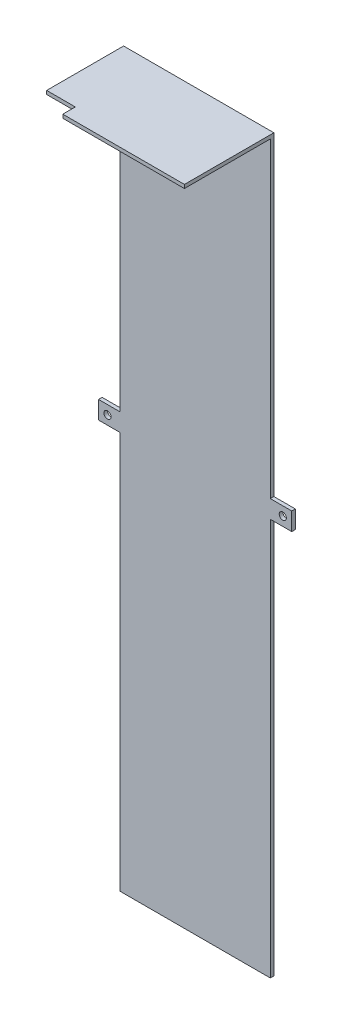
SolidWorks part; units mm, degrees
ref_plane "Alzado" through (0, 0, 0) normal (0, 0, 1) x (1, 0, 0)
ref_plane "Planta" through (0, 0, 0) normal (0, 1, 0) x (1, 0, 0)
ref_plane "Vista lateral" through (0, 0, 0) normal (1, 0, 0) x (0, 0, -1)
sketch "Sketch1" plane through (0, 0, 0) normal (0, 1, 0) x (1, 0, 0)
  line L1 (-16.6842, 5.7368) -> (25.3158, 5.7368)
  line L2 (-16.6842, 5.7368) -> (-16.6842, -19.2632)
  line L3 (-16.6842, -19.2632) -> (25.3158, -19.2632)
  line L4 (25.3158, 5.7368) -> (25.3158, -19.2632)
  dimension "D1" = 42
  dimension "D2" = 25
extrude "Boss-Extrude1" add sketch "Sketch1" along normal blind 1
sketch "Sketch2" plane through (0, 1, 0) normal (0, 1, 0) x (1, 0, 0)
  line L0 (-16.6842, 5.7368) -> (-16.6842, -19.2632) construction
  line L1 (25.3158, 5.7368) -> (-16.6842, 5.7368)
  line L2 (25.3158, 5.7368) -> (25.3158, 4.7368)
  line L3 (25.3158, 4.7368) -> (-16.6842, 4.7368)
  line L4 (-16.6842, 5.7368) -> (-16.6842, 4.7368)
  dimension "D1" = 1
extrude "Boss-Extrude2" add sketch "Sketch2" against normal blind 179
sketch "Sketch3" plane through (0, -178, 0) normal (0, -1, 0) x (1, 0, 0)
  line L1 (25.3158, -5.7368) -> (-16.6842, -5.7368)
  line L2 (25.3158, -5.7368) -> (25.3158, -4.7368)
  line L3 (25.3158, -4.7368) -> (-16.6842, -4.7368)
  line L4 (-16.6842, -5.7368) -> (-16.6842, -4.7368)
extrude "Boss-Extrude3" add sketch "Sketch3" along normal blind 2.1
sketch "Sketch4" plane through (0, 0, -4.7368) normal (0, 0, 1) x (1, 0, 0)
  line L0 (-16.6842, -180.1) -> (-16.6842, 0) construction
  line L1 (25.3158, -180.1) -> (-16.6842, -180.1)
  line L2 (25.3158, -180.1) -> (25.3158, -179.1)
  line L3 (25.3158, -179.1) -> (-16.6842, -179.1)
  line L4 (-16.6842, -180.1) -> (-16.6842, -179.1)
  dimension "D1" = 1
extrude "Boss-Extrude4" add sketch "Sketch4" along normal blind 15
sketch "Sketch6" plane through (0, -180.1, 0) normal (0, -1, 0) x (1, 0, 0)
  line L0 (-16.6842, 10.2632) -> (-16.6842, -5.7368) construction
  line L2 (25.3158, -5.7368) -> (25.3158, 10.2632) construction
  circle A0 centre (-6.6842, 3.5932) radius 1.25
  circle A1 centre (15.3158, 3.5932) radius 1.25
  dimension "D2" = 10
  dimension "D1" = 10
extrude "Cut-Extrude1" cut sketch "Sketch6" against normal blind 15
sketch "Sketch7" plane through (0, -180.1, 0) normal (0, -1, 0) x (1, 0, 0)
  line L1 (25.3158, -5.7368) -> (25.3158, 10.2632) construction
  line L2 (-16.6842, 10.2632) -> (25.3158, 10.2632)
  line L3 (-16.6842, 10.2632) -> (-16.6842, 8.5932)
  line L4 (-16.6842, 8.5932) -> (25.3158, 8.5932)
  line L5 (25.3158, 10.2632) -> (25.3158, 8.5932)
extrude "Cut-Extrude2" cut sketch "Sketch7" against normal blind 15
sketch "Sketch8" plane through (0, 1, 0) normal (0, 1, 0) x (1, 0, 0)
  line L1 (-16.6842, -19.2632) -> (-8.6842, -19.2632)
  line L2 (-16.6842, -19.2632) -> (-16.6842, -15.7632)
  line L3 (-16.6842, -15.7632) -> (-8.6842, -15.7632)
  line L4 (-8.6842, -19.2632) -> (-8.6842, -15.7632)
  dimension "D1" = 8
  dimension "D2" = 3.5
extrude "Cut-Extrude3" cut sketch "Sketch8" against normal blind 15
sketch "Sketch9" plane through (0, -180.1, 0) normal (0, -1, 0) x (1, 0, 0)
  line L1 (-16.6842, 8.5932) -> (25.3158, 8.5932)
  line L2 (-16.6842, 8.5932) -> (-16.6842, -5.7368)
  line L3 (-16.6842, -5.7368) -> (25.3158, -5.7368)
  line L4 (25.3158, 8.5932) -> (25.3158, -5.7368)
extrude "Cut-Extrude4" cut sketch "Sketch9" against normal blind 10
sketch "Sketch10" plane through (0, 0, -5.7368) normal (0, 0, -1) x (-1, 0, 0)
  line L0 (-25.3158, -170.1) -> (-6.8158, -170.1) construction
  line L1 (16.6842, -170.1) -> (-25.3158, -170.1) construction
  line L3 (-6.8158, -170.1) -> (-1.8158, -170.1)
  line L4 (-6.8158, -170.1) -> (-6.8158, -176.1)
  line L5 (-6.8158, -176.1) -> (-1.8158, -176.1)
  line L6 (-1.8158, -170.1) -> (-1.8158, -176.1)
  dimension "D1" = 18.5
  dimension "D2" = 6
  dimension "D3" = 5
extrude "Boss-Extrude5" add sketch "Sketch10" against normal blind 1
sketch "Sketch11" plane through (0, 0, -5.7368) normal (0, 0, -1) x (-1, 0, 0)
  line L0 (-6.8158, -176.1) -> (-6.8158, -171.1) construction
  line L1 (-6.8158, -170.1) -> (-6.8158, -176.1) construction
  line L2 (-6.8158, -171.1) -> (-1.8158, -171.1) construction
  line L3 (-1.8158, -176.1) -> (-1.8158, -170.1) construction
  line L4 (-1.8158, -171.1) -> (-1.8158, -176.1) construction
  line L5 (-1.8158, -176.1) -> (-6.8158, -176.1) construction
  circle A0 centre (-4.3158, -173.6) radius 1
  dimension "D1" = 5
extrude "Cut-Extrude5" cut sketch "Sketch11" against normal blind 1
sketch "Sketch12" plane through (0, -170.1, 0) normal (0, -1, 0) x (1, 0, 0)
  line L1 (25.3158, -5.7368) -> (-16.6842, -5.7368)
  line L2 (25.3158, -5.7368) -> (25.3158, -4.7368)
  line L3 (25.3158, -4.7368) -> (-16.6842, -4.7368)
  line L4 (-16.6842, -5.7368) -> (-16.6842, -4.7368)
extrude "Boss-Extrude6" add sketch "Sketch12" along normal blind 9
sketch "Sketch13" plane through (0, 0, -5.7368) normal (0, 0, -1) x (-1, 0, 0)
  line L0 (16.6842, -179.1) -> (-25.3158, -179.1) construction
  line L1 (-6.8158, -179.1) -> (-1.8158, -179.1)
  line L2 (-6.8158, -179.1) -> (-6.8158, -185.1)
  line L3 (-6.8158, -185.1) -> (-1.8158, -185.1)
  line L4 (-1.8158, -179.1) -> (-1.8158, -185.1)
  line L5 (-25.3158, 1) -> (-25.3158, -179.1) construction
  dimension "D1" = 6
  dimension "D2" = 5
  dimension "D3" = 18.5
extrude "Boss-Extrude8" add sketch "Sketch13" against normal blind 1
sketch "Sketch15" plane through (0, 0, -5.7368) normal (0, 0, -1) x (-1, 0, 0)
  line L0 (-1.8158, -185.1) -> (-1.8158, -180.1) construction
  line L1 (-1.8158, -185.1) -> (-1.8158, -179.1) construction
  line L2 (-1.8158, -180.1) -> (-6.8158, -180.1) construction
  line L3 (-6.8158, -179.1) -> (-6.8158, -185.1) construction
  line L4 (-6.8158, -180.1) -> (-6.8158, -185.1) construction
  line L5 (-6.8158, -185.1) -> (-1.8158, -185.1) construction
  circle A0 centre (-4.3158, -182.6) radius 1
  dimension "D1" = 5
extrude "Cut-Extrude7" cut sketch "Sketch15" against normal blind 1
sketch "Sketch16" plane through (0, 0, -5.7368) normal (0, 0, -1) x (-1, 0, 0)
  line L0 (-25.3158, -179.1) -> (-25.3158, -92.05) construction
  line L1 (-25.3158, 1) -> (-25.3158, -179.1) construction
  line L3 (-25.3158, -92.05) -> (-31.3158, -92.05)
  line L4 (-25.3158, -92.05) -> (-25.3158, -87.05)
  line L5 (-25.3158, -87.05) -> (-31.3158, -87.05)
  line L6 (-31.3158, -92.05) -> (-31.3158, -87.05)
  dimension "D1" = 87.05
  dimension "D2" = 6
  dimension "D3" = 5
extrude "Boss-Extrude9" add sketch "Sketch16" against normal blind 1
sketch "Sketch17" plane through (0, 0, -5.7368) normal (0, 0, -1) x (-1, 0, 0)
  line L1 (-31.3158, -87.05) -> (21.6842, -87.05)
  line L2 (-31.3158, -87.05) -> (-31.3158, -92.05)
  line L3 (-31.3158, -92.05) -> (21.6842, -92.05)
  line L4 (21.6842, -87.05) -> (21.6842, -92.05)
  dimension "D1" = 53
extrude "Boss-Extrude10" add sketch "Sketch17" against normal blind 1
sketch "Sketch18" plane through (0, 0, -5.7368) normal (0, 0, -1) x (-1, 0, 0)
  line L0 (-31.3158, -87.05) -> (-26.3158, -87.05) construction
  line L1 (-25.3158, -87.05) -> (-31.3158, -87.05) construction
  line L2 (-26.3158, -87.05) -> (-26.3158, -92.05) construction
  line L3 (-31.3158, -92.05) -> (-25.3158, -92.05) construction
  line L4 (-26.3158, -92.05) -> (-31.3158, -92.05) construction
  line L5 (-31.3158, -92.05) -> (-31.3158, -87.05) construction
  circle A0 centre (-28.8158, -89.55) radius 1
  dimension "D1" = 5
extrude "Cut-Extrude8" cut sketch "Sketch18" against normal blind 1
sketch "Sketch20" plane through (-21.6842, 0, 0) normal (-1, 0, 0) x (0, 0, 1)
  line L1 (-5.7368, -87.05) -> (-4.7368, -87.05)
  line L2 (-5.7368, -87.05) -> (-5.7368, -92.05)
  line L3 (-5.7368, -92.05) -> (-4.7368, -92.05)
  line L4 (-4.7368, -87.05) -> (-4.7368, -92.05)
extrude "Boss-Extrude11" add sketch "Sketch20" along normal blind 1
sketch "Sketch21" plane through (0, 0, -5.7368) normal (0, 0, -1) x (-1, 0, 0)
  line L0 (22.6842, -87.05) -> (17.6842, -87.05) construction
  line L1 (22.6842, -87.05) -> (16.6842, -87.05) construction
  line L2 (17.6842, -87.05) -> (17.6842, -92.05) construction
  line L3 (16.6842, -92.05) -> (22.6842, -92.05) construction
  line L4 (17.6842, -92.05) -> (22.6842, -92.05) construction
  line L5 (22.6842, -92.05) -> (22.6842, -87.05) construction
  circle A0 centre (20.1842, -89.55) radius 1
  dimension "D2" = 2.5
  dimension "D1" = 5
extrude "Cut-Extrude9" cut sketch "Sketch21" against normal blind 1
sketch "Sketch22" plane through (0, -179.1, 0) normal (0, -1, 0) x (1, 0, 0)
  line L1 (-16.6842, -5.7368) -> (25.3158, -5.7368)
  line L2 (-16.6842, -5.7368) -> (-16.6842, -4.7368)
  line L3 (-16.6842, -4.7368) -> (25.3158, -4.7368)
  line L4 (25.3158, -5.7368) -> (25.3158, -4.7368)
extrude "Boss-Extrude13" add sketch "Sketch22" along normal blind 24
